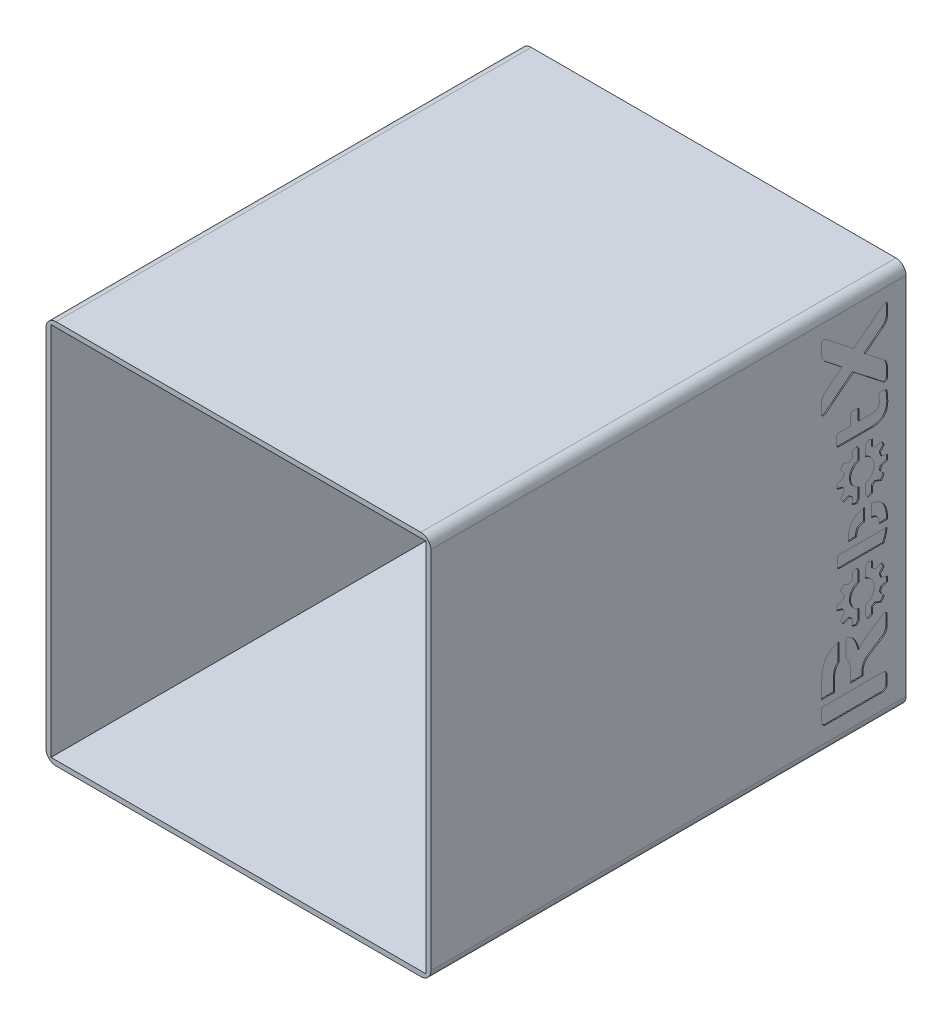
SolidWorks part; units mm, degrees
ref_plane "Спереди" through (0, 0, 0) normal (0, 0, 1) x (1, 0, 0)
ref_plane "Сверху" through (0, 0, 0) normal (0, 1, 0) x (1, 0, 0)
ref_plane "Справа" through (0, 0, 0) normal (1, 0, 0) x (0, 0, -1)
sketch "Эскиз1" plane through (0, 0, 0) normal (0, 0, 1) x (1, 0, 0)
  line L1 (-57.5, 57.5) -> (57.5, 57.5)
  line L2 (-57.5, 57.5) -> (-57.5, -57.5)
  line L3 (-57.5, -57.5) -> (57.5, -57.5)
  line L4 (57.5, 57.5) -> (57.5, -57.5)
  line L5 (-57.5, 57.5) -> (57.5, -57.5) construction
  line L6 (-57.5, -57.5) -> (57.5, 57.5) construction
  point P0 (0, 0)
  dimension "D1" = 115
  dimension "D2" = 115
extrude "Бобышка-Вытянуть1" add sketch "Эскиз1" along normal blind 2
sketch "Эскиз2" plane through (0, 0, 2) normal (0, 0, 1) x (1, 0, 0)
  line L0 (56, -56) -> (56, 56)
  line L1 (56, 56) -> (-56, 56)
  line L2 (-56, 56) -> (-56, -56)
  line L3 (-56, -56) -> (56, -56)
  line L4 (57.5, -57.5) -> (57.5, 57.5)
  line L5 (57.5, 57.5) -> (-57.5, 57.5)
  line L6 (-57.5, 57.5) -> (-57.5, -57.5)
  line L7 (-57.5, -57.5) -> (57.5, -57.5)
  line L8 (57.5, -57.5) -> (57.5, 57.5)
  line L9 (57.5, 57.5) -> (-57.5, 57.5)
  line L10 (-57.5, 57.5) -> (-57.5, -57.5)
  line L11 (-57.5, -57.5) -> (57.5, -57.5)
  dimension "D1" = 0
  dimension "D2" = 1.5
extrude "Бобышка-Вытянуть2" add sketch "Эскиз2" along normal blind 140
fillet "Скругление1" radius 3 4 edges at (-57.5, 57.5, 71) (57.5, 57.5, 71) (57.5, -57.5, 71) (-57.5, -57.5, 71)
sketch "Эскиз3" plane through (57.5, 0, 0) normal (1, 0, 0) x (0, 0, -1)
  line L0 (-11.0806, -38.2738) -> (-6.9696, -35.679)
  line L1 (-5.6732, -33.3277) -> (-5.6732, -30.2461)
  line L2 (-6.6892, -29.686) -> (-10.8771, -32.3294)
  line L3 (-25.1806, -37.3777) -> (-25.1806, -42.7406)
  line L4 (-23.9003, -49.8609) -> (-6.9535, -49.8609)
  line L5 (-5.6732, -48.5806) -> (-5.6732, -46.0209)
  line L6 (-6.9535, -44.7406) -> (-25.1806, -44.7406)
  line L7 (-12.8091, -42.7406) -> (-12.8091, -41.4089)
  line L8 (-16.6374, -38.9524) -> (-16.6374, -42.7406)
  line L9 (-21.3403, -42.7406) -> (-21.3403, -38.9524)
  line L10 (-5.6304, -7.8281) -> (-19.8958, -7.8281)
  line L11 (-20.5379, -8.4632) -> (-20.5379, -10.7706)
  line L12 (-19.8958, -11.4057) -> (-6.6508, -11.4057)
  line L13 (-6.3023, 28.1333) -> (-7.4192, 28.1333)
  line L14 (-8.0636, 27.489) -> (-8.0636, 27.1024)
  line L15 (-10.1685, 23.8162) -> (-14.0131, 23.8162)
  line L16 (-14.0131, 23.8162) -> (-14.0131, 26.7372)
  line L17 (-14.6575, 27.3816) -> (-15.9032, 27.3816)
  line L18 (-16.5476, 26.7372) -> (-16.5476, 23.8162)
  line L19 (-16.5476, 23.8162) -> (-20.0665, 23.8162)
  line L20 (-20.7144, 23.1718) -> (-20.7144, 20.8306)
  line L21 (-20.0665, 20.1863) -> (-10.1685, 20.1863)
  line L22 (-25.2171, 34.1924) -> (-25.2171, 31.2503)
  line L23 (-23.9235, 30.774) -> (-15.6764, 37.2745)
  line L24 (-15.6764, 37.2745) -> (-6.8689, 30.3817)
  line L25 (-5.5753, 30.8581) -> (-5.5753, 33.7721)
  line L26 (-6.8689, 36.1537) -> (-12.1973, 40.3287)
  line L27 (-12.1973, 40.3287) -> (-6.8689, 44.5036)
  line L28 (-5.5753, 46.8853) -> (-5.5753, 49.7993)
  line L29 (-6.8689, 50.2756) -> (-15.6764, 43.3828)
  line L30 (-15.6764, 43.3828) -> (-23.9235, 49.8834)
  line L31 (-25.2171, 49.407) -> (-25.2171, 46.4649)
  line L32 (-23.9235, 44.0833) -> (-19.1555, 40.3287)
  line L33 (-19.1555, 40.3287) -> (-23.9235, 36.574)
  line L34 (-21.3403, -38.9524) -> (-16.6374, -38.9524) construction
  line L35 (-18.9889, -38.9524) -> (-18.9889, -35.4182) construction
  line L36 (-11.4148, 17.5578) -> (-12.0387, 16.6321)
  line L37 (-11.4148, 2.7678) -> (-12.0387, 3.6934)
  line L38 (-7.3783, 5.1346) -> (-9.161, 5.7842)
  line L39 (-5.5038, 9.422) -> (-7.3279, 8.8997)
  line L40 (-20.5736, 9.422) -> (-18.7495, 8.8997)
  line L41 (-19.57, 6.3332) -> (-18.4013, 7.8279)
  line L42 (-18.6991, 15.191) -> (-16.9164, 14.5414)
  line L43 (-5.5038, 10.9036) -> (-7.3279, 11.4259)
  line L44 (-14.6626, 2.7678) -> (-14.0387, 3.6934)
  line L45 (-16.0716, 17.0999) -> (-16.0047, 15.2038)
  line L46 (-6.5074, 13.9923) -> (-7.6761, 12.4976)
  line L47 (-19.57, 13.9923) -> (-18.4013, 12.4976)
  line L48 (-7.3783, 15.191) -> (-9.161, 14.5414)
  line L49 (-16.0716, 3.2256) -> (-16.0047, 5.1218)
  line L50 (-14.6626, 17.5578) -> (-14.0387, 16.6321)
  line L51 (-10.0058, 17.0999) -> (-10.0727, 15.2038)
  line L52 (-10.0058, 3.2256) -> (-10.0727, 5.1218)
  line L53 (-6.5074, 6.3332) -> (-7.6761, 7.8279)
  line L54 (-20.5736, 10.9036) -> (-18.7495, 11.4259)
  line L55 (-18.6991, 5.1346) -> (-16.9164, 5.7842)
  line L56 (-12.8091, -42.7406) -> (-16.6374, -42.7406)
  line L57 (-25.1806, -44.7406) -> (-25.1806, -48.5806)
  line L58 (-18.9889, -35.4182) -> (-18.9889, -30.2816) construction
  line L59 (-17.9889, -35.77) -> (-17.9889, -30.3713)
  line L60 (-19.9889, -35.6683) -> (-19.9889, -30.3497)
  line L61 (-21.3403, -42.7406) -> (-25.1806, -42.7406)
  line L62 (-5.4865, -5.8281) -> (-7.986, -5.8281)
  line L63 (-16.0716, -14.372) -> (-16.0047, -16.2682)
  line L64 (-11.3504, -2.9803) -> (-11.3504, 0.7032) construction
  line L65 (-10.3504, -3.0339) -> (-10.3504, 0.6493)
  line L66 (-12.3504, -3.0326) -> (-12.3504, 0.6501)
  line L67 (-12.0387, 3.6934) -> (-12.0387, 6.7635)
  line L68 (-14.7286, -5.8281) -> (-17.1799, -5.8281)
  line L69 (-14.0387, 3.6934) -> (-14.0387, 6.7635)
  line L70 (-10.0058, -28.2463) -> (-10.0727, -26.3502)
  line L71 (-18.6991, -16.281) -> (-16.9164, -16.9306)
  line L72 (-14.0387, 13.5621) -> (-14.0387, 16.6321)
  line L73 (-12.0387, 13.5621) -> (-12.0387, 16.6321)
  line L74 (-12.0387, -17.9099) -> (-12.0387, -14.8398)
  line L75 (-16.0716, -28.2463) -> (-16.0047, -26.3502)
  line L76 (-5.5038, -22.05) -> (-7.3279, -22.5723)
  line L77 (-12.0387, -27.7785) -> (-12.0387, -24.7085)
  line L78 (-11.4148, -13.9142) -> (-12.0387, -14.8398)
  line L79 (-6.5074, -17.4796) -> (-7.6761, -18.9743)
  line L80 (-6.5074, -25.1388) -> (-7.6761, -23.6441)
  line L81 (-5.5038, -20.5684) -> (-7.3279, -20.0461)
  line L82 (-14.6626, -13.9142) -> (-14.0387, -14.8398)
  line L83 (-20.5736, -22.05) -> (-18.7495, -22.5723)
  line L84 (-14.0387, -27.7785) -> (-14.0387, -24.7085)
  line L85 (-19.57, -17.4796) -> (-18.4013, -18.9743)
  line L86 (-11.4148, -28.7042) -> (-12.0387, -27.7785)
  line L87 (-20.5736, -20.5684) -> (-18.7495, -20.0461)
  line L88 (-14.6626, -28.7042) -> (-14.0387, -27.7785)
  line L89 (-10.0058, -14.372) -> (-10.0727, -16.2682)
  line L90 (-19.57, -25.1388) -> (-18.4013, -23.6441)
  line L91 (-14.0387, -17.9099) -> (-14.0387, -14.8398)
  line L92 (-7.3783, -16.281) -> (-9.161, -16.9306)
  line L93 (-7.3783, -26.3374) -> (-9.161, -25.6878)
  line L94 (-18.6991, -26.3374) -> (-16.9164, -25.6878)
  arc A0 (-10.0058, 17.0999) -> (-11.4148, 17.5578) centre (-13.0387, 10.1628) ccw
  arc A1 (-18.4013, 12.4976) -> (-18.7495, 11.4259) centre (-13.0387, 10.1628) ccw
  arc A2 (-20.5736, 10.9036) -> (-20.5736, 9.422) centre (-13.0387, 10.1628) ccw
  arc A3 (-11.4148, 2.7678) -> (-10.0058, 3.2256) centre (-13.0387, 10.1628) ccw
  arc A4 (-7.3279, 11.4259) -> (-7.6761, 12.4976) centre (-13.0387, 10.1628) ccw
  arc A5 (-6.5074, 13.9923) -> (-7.3783, 15.191) centre (-13.0387, 10.1628) ccw
  arc A6 (-16.0047, 15.2038) -> (-16.9164, 14.5414) centre (-13.0387, 10.1628) ccw
  arc A7 (-16.9164, 5.7842) -> (-16.0047, 5.1218) centre (-13.0387, 10.1628) ccw
  arc A8 (-18.6991, 15.191) -> (-19.57, 13.9923) centre (-13.0387, 10.1628) ccw
  arc A9 (-7.6761, 7.8279) -> (-7.3279, 8.8997) centre (-13.0387, 10.1628) ccw
  arc A10 (-16.0716, 3.2256) -> (-14.6626, 2.7678) centre (-13.0387, 10.1628) ccw
  arc A11 (-14.0387, 13.5621) -> (-14.0387, 6.7635) centre (-13.0387, 10.1628) ccw
  arc A12 (-10.0727, 5.1218) -> (-9.161, 5.7842) centre (-13.0387, 10.1628) ccw
  arc A13 (-5.5038, 9.422) -> (-5.5038, 10.9036) centre (-13.0387, 10.1628) ccw
  arc A14 (-14.6626, 17.5578) -> (-16.0716, 17.0999) centre (-13.0387, 10.1628) ccw
  arc A15 (-19.57, 6.3332) -> (-18.6991, 5.1346) centre (-13.0387, 10.1628) ccw
  arc A16 (-18.7495, 8.8997) -> (-18.4013, 7.8279) centre (-13.0387, 10.1628) ccw
  arc A17 (-7.3783, 5.1346) -> (-6.5074, 6.3332) centre (-13.0387, 10.1628) ccw
  arc A18 (-9.161, 14.5414) -> (-10.0727, 15.2038) centre (-13.0387, 10.1628) ccw
  arc A19 (-25.1806, -48.5806) -> (-23.9003, -49.8609) centre (-23.9003, -48.5806) ccw
  arc A20 (-5.6732, -48.5806) -> (-6.9535, -49.8609) centre (-6.9535, -48.5806) cw
  arc A21 (-6.9535, -44.7406) -> (-5.6732, -46.0209) centre (-6.9535, -46.0209) cw
  arc A22 (-5.6732, -30.2461) -> (-6.6892, -29.686) centre (-6.3356, -30.2461) ccw
  arc A23 (-5.6732, -33.3277) -> (-6.9696, -35.679) centre (-8.4538, -33.3277) cw
  arc A24 (-11.0806, -38.2738) -> (-12.8091, -41.4089) centre (-9.1017, -41.4089) ccw
  arc A25 (-12.0387, 6.7635) -> (-12.0387, 13.5621) centre (-13.0387, 10.1628) ccw
  arc A26 (-20.5736, -20.5684) -> (-20.5736, -22.05) centre (-13.0387, -21.3092) ccw
  arc A27 (-12.0387, -24.7085) -> (-12.0387, -17.9099) centre (-13.0387, -21.3092) ccw
  arc A28 (-7.6761, -23.6441) -> (-7.3279, -22.5723) centre (-13.0387, -21.3092) ccw
  arc A29 (-18.7495, -22.5723) -> (-18.4013, -23.6441) centre (-13.0387, -21.3092) ccw
  arc A30 (-16.0047, -16.2682) -> (-16.9164, -16.9306) centre (-13.0387, -21.3092) ccw
  arc A31 (-5.5038, -22.05) -> (-5.5038, -20.5684) centre (-13.0387, -21.3092) ccw
  arc A32 (-11.4148, -28.7042) -> (-10.0058, -28.2463) centre (-13.0387, -21.3092) ccw
  arc A33 (-16.0716, -28.2463) -> (-14.6626, -28.7042) centre (-13.0387, -21.3092) ccw
  arc A34 (-10.0058, -14.372) -> (-11.4148, -13.9142) centre (-13.0387, -21.3092) ccw
  arc A35 (-7.3783, -26.3374) -> (-6.5074, -25.1388) centre (-13.0387, -21.3092) ccw
  arc A36 (-16.9164, -25.6878) -> (-16.0047, -26.3502) centre (-13.0387, -21.3092) ccw
  arc A37 (-14.6626, -13.9142) -> (-16.0716, -14.372) centre (-13.0387, -21.3092) ccw
  arc A38 (-7.3279, -20.0461) -> (-7.6761, -18.9743) centre (-13.0387, -21.3092) ccw
  arc A39 (-14.0387, -17.9099) -> (-14.0387, -24.7085) centre (-13.0387, -21.3092) ccw
  arc A40 (-18.4013, -18.9743) -> (-18.7495, -20.0461) centre (-13.0387, -21.3092) ccw
  arc A41 (-9.161, -16.9306) -> (-10.0727, -16.2682) centre (-13.0387, -21.3092) ccw
  arc A42 (-18.6991, -16.281) -> (-19.57, -17.4796) centre (-13.0387, -21.3092) ccw
  arc A43 (-19.57, -25.1388) -> (-18.6991, -26.3374) centre (-13.0387, -21.3092) ccw
  arc A44 (-6.5074, -17.4796) -> (-7.3783, -16.281) centre (-13.0387, -21.3092) ccw
  arc A45 (-10.0727, -26.3502) -> (-9.161, -25.6878) centre (-13.0387, -21.3092) ccw
  spline S0 degree 3 poles (-21.3403, -38.9524) (-21.3403, -37.1939) (-20.7506, -36.1217) (-19.9889, -35.6683) knots 0 0 0 0 0.354104 0.354104 0.354104 0.354104
  spline S1 degree 3 poles (-25.1806, -37.3777) (-25.1806, -32.6212) (-22.5564, -30.717) (-19.9889, -30.3497) knots 0 0 0 0 0.503092 0.503092 0.503092 0.503092
  spline S2 degree 3 poles (-17.9889, -30.3713) (-16.2757, -30.6931) (-14.84, -31.9583) (-14.0298, -35.4099) knots 0.637572 0.637572 0.637572 0.637572 1 1 1 1
  spline S3 degree 3 poles (-17.9889, -35.77) (-17.2271, -36.2904) (-16.6374, -37.3737) (-16.6374, -38.9524) knots 0.645896 0.645896 0.645896 0.645896 1 1 1 1
  spline S4 degree 3 poles (-10.8771, -32.3294) (-12.6332, -33.4378) (-13.6094, -34.27) (-14.0298, -35.4099) knots 0.333333 0.333333 0.333333 0.333333 0.388889 0.388889 0.388889 0.388889
  spline S5 degree 3 poles (-14.7286, -5.8281) (-14.7345, -5.7409) (-14.7375, -5.6593) (-14.7375, -5.5841) knots 0.142989 0.142989 0.142989 0.142989 0.166667 0.166667 0.166667 0.166667
  spline S6 degree 3 poles (-14.7375, -5.5841) (-14.7375, -3.9745) (-13.9971, -3.2261) (-12.3504, -3.0326) knots 0.166667 0.166667 0.166667 0.166667 0.307474 0.307474 0.307474 0.307474
  spline S7 degree 3 poles (-10.3504, -3.0339) (-8.7223, -3.2303) (-7.9845, -3.9872) (-7.9845, -5.6476) knots 0.359435 0.359435 0.359435 0.359435 0.5 0.5 0.5 0.5
  spline S8 degree 3 poles (-7.9845, -5.6476) (-7.9845, -5.708) (-7.985, -5.7682) (-7.986, -5.8281) knots 0.5 0.5 0.5 0.5 0.511595 0.511595 0.511595 0.511595
  spline S9 degree 3 poles (-6.6508, -11.4057) (-6.2155, -10.6512) (-5.8299, -9.27) (-5.6304, -7.8281) knots 0 0 0 0 0.062314 0.062314 0.062314 0.062314
  spline S10 degree 3 poles (-5.4865, -5.8281) (-5.4901, -4.217) (-5.7691, -2.899) (-6.3183, -1.8797) knots 0.091493 0.091493 0.091493 0.091493 0.181818 0.181818 0.181818 0.181818
  spline S11 degree 3 poles (-6.3183, -1.8797) (-7.1085, -0.4129) (-8.458, 0.4355) (-10.3504, 0.6493) knots 0.181818 0.181818 0.181818 0.181818 0.259648 0.259648 0.259648 0.259648
  spline S12 degree 3 poles (-12.3504, 0.6501) (-15.5858, 0.293) (-17.2355, -1.8364) (-17.2355, -4.8432) knots 0.280864 0.280864 0.280864 0.280864 0.363636 0.363636 0.363636 0.363636
  spline S13 degree 3 poles (-17.2355, -4.8432) (-17.2355, -5.2019) (-17.2152, -5.5269) (-17.1799, -5.8281) knots 0.363636 0.363636 0.363636 0.363636 0.389311 0.389311 0.389311 0.389311
  spline S14 degree 3 poles (-19.8958, -7.8281) (-20.2592, -7.8281) (-20.5379, -8.1033) (-20.5379, -8.4632) knots 0.545455 0.545455 0.545455 0.545455 0.636364 0.636364 0.636364 0.636364
  spline S15 degree 3 poles (-20.5379, -10.7706) (-20.5379, -11.1305) (-20.2592, -11.4057) (-19.8958, -11.4057) knots 0.727273 0.727273 0.727273 0.727273 0.818182 0.818182 0.818182 0.818182
  spline S16 degree 3 poles (-5.658, 27.489) (-5.7224, 27.8541) (-5.9801, 28.1333) (-6.3023, 28.1333) knots 0 0 0 0 0.05 0.05 0.05 0.05
  spline S17 degree 3 poles (-7.4192, 28.1333) (-7.7843, 28.1333) (-8.0636, 27.8541) (-8.0636, 27.489) knots 0.1 0.1 0.1 0.1 0.15 0.15 0.15 0.15
  spline S18 degree 3 poles (-8.0636, 27.1024) (-8.0636, 26.6298) (-7.9347, 26.2217) (-7.9347, 25.6633) knots 0.2 0.2 0.2 0.2 0.25 0.25 0.25 0.25
  spline S19 degree 3 poles (-7.9347, 25.6633) (-7.9347, 24.5679) (-8.7079, 23.8162) (-10.1685, 23.8162) knots 0.25 0.25 0.25 0.25 0.3 0.3 0.3 0.3
  spline S20 degree 3 poles (-14.0131, 26.7372) (-14.0131, 27.1024) (-14.2923, 27.3816) (-14.6575, 27.3816) knots 0.4 0.4 0.4 0.4 0.45 0.45 0.45 0.45
  spline S21 degree 3 poles (-15.9032, 27.3816) (-16.2684, 27.3816) (-16.5476, 27.1024) (-16.5476, 26.7372) knots 0.5 0.5 0.5 0.5 0.55 0.55 0.55 0.55
  spline S22 degree 3 poles (-20.0665, 23.8162) (-20.4316, 23.8162) (-20.7144, 23.5369) (-20.7144, 23.1718) knots 0.65 0.65 0.65 0.65 0.7 0.7 0.7 0.7
  spline S23 degree 3 poles (-20.7144, 20.8306) (-20.7144, 20.4655) (-20.4316, 20.1863) (-20.0665, 20.1863) knots 0.75 0.75 0.75 0.75 0.8 0.8 0.8 0.8
  spline S24 degree 3 poles (-10.1685, 20.1863) (-6.9467, 20.1863) (-5.4432, 21.6898) (-5.4432, 24.6968) knots 0.85 0.85 0.85 0.85 0.9 0.9 0.9 0.9
  spline S25 degree 3 poles (-5.4432, 24.6968) (-5.4432, 25.6633) (-5.5291, 26.8446) (-5.658, 27.489) knots 0.9 0.9 0.9 0.9 1 1 1 1
  spline S26 degree 3 poles (-23.9235, 36.574) (-24.596, 36.0417) (-25.2171, 35.3132) (-25.2171, 34.1924) knots 0 0 0 0 0.047619 0.047619 0.047619 0.047619
  spline S27 degree 3 poles (-25.2171, 31.2503) (-25.2171, 30.5218) (-24.596, 30.2416) (-23.9235, 30.774) knots 0.095238 0.095238 0.095238 0.095238 0.142857 0.142857 0.142857 0.142857
  spline S28 degree 3 poles (-6.8689, 30.3817) (-6.1965, 29.8493) (-5.5753, 30.1296) (-5.5753, 30.8581) knots 0.238095 0.238095 0.238095 0.238095 0.285714 0.285714 0.285714 0.285714
  spline S29 degree 3 poles (-5.5753, 33.7721) (-5.5753, 34.8929) (-6.1965, 35.6214) (-6.8689, 36.1537) knots 0.333333 0.333333 0.333333 0.333333 0.380952 0.380952 0.380952 0.380952
  spline S30 degree 3 poles (-6.8689, 44.5036) (-6.1965, 45.036) (-5.5753, 45.7645) (-5.5753, 46.8853) knots 0.47619 0.47619 0.47619 0.47619 0.52381 0.52381 0.52381 0.52381
  spline S31 degree 3 poles (-5.5753, 49.7993) (-5.5753, 50.5278) (-6.1965, 50.808) (-6.8689, 50.2756) knots 0.571429 0.571429 0.571429 0.571429 0.619048 0.619048 0.619048 0.619048
  spline S32 degree 3 poles (-23.9235, 49.8834) (-24.596, 50.4157) (-25.2171, 50.1355) (-25.2171, 49.407) knots 0.714286 0.714286 0.714286 0.714286 0.761905 0.761905 0.761905 0.761905
  spline S33 degree 3 poles (-25.2171, 46.4649) (-25.2171, 45.3442) (-24.596, 44.6157) (-23.9235, 44.0833) knots 0.809524 0.809524 0.809524 0.809524 0.857143 0.857143 0.857143 0.857143
  point P39 (-13.0387, 10.1628)
  point P168 (-13.0387, -21.3092)
extrude "Вырез-Вытянуть1" cut sketch "Эскиз3" against normal blind 0.3
